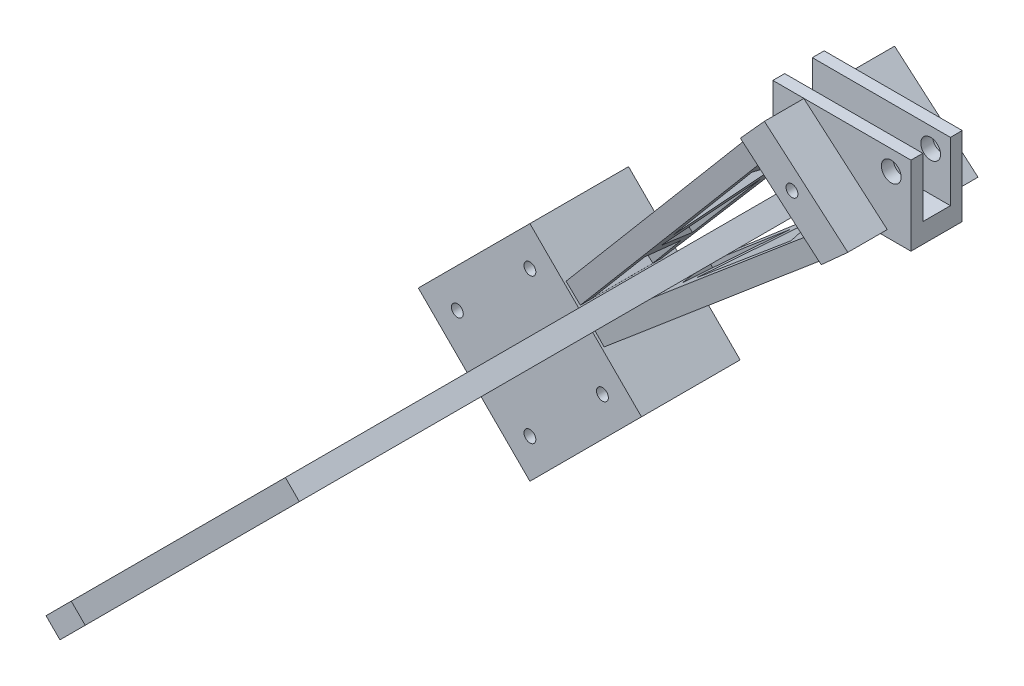
SolidWorks part; units mm, degrees
ref_plane "Front Plane" through (0, 0, 0) normal (0, 0, 1) x (1, 0, 0)
ref_plane "Top Plane" through (0, 0, 0) normal (0, 1, 0) x (1, 0, 0)
ref_plane "Right Plane" through (0, 0, 0) normal (1, 0, 0) x (0, 0, -1)
sketch "Sketch10" plane through (0, 0, 0) normal (0, 0, 1) x (1, 0, 0)
  line L1 (-17.5, 10) -> (17.5, 10)
  line L2 (-17.5, 10) -> (-17.5, -10)
  line L3 (-17.5, -10) -> (17.5, -10)
  line L4 (17.5, 10) -> (17.5, -10)
  line L5 (-17.5, 10) -> (17.5, -10) construction
  line L6 (-17.5, -10) -> (17.5, 10) construction
  point P0 (0, 0)
  dimension "D1" = 35
  dimension "D2" = 20
extrude "Boss-Extrude9" add sketch "Sketch10" along normal mid plane 13
sketch "Sketch11" plane through (-17.5, 0, 0) normal (-1, 0, 0) x (0, 0, 1)
  line L0 (6.5, 10) -> (-6.5, 10) construction
  line L2 (3.5, -5) -> (3.5, 10)
  line L3 (3.5, 10) -> (-3.5, 10)
  line L4 (-3.5, -5) -> (-3.5, 10)
  line L5 (1.75, -5) -> (-3.5, 10) construction
  line L6 (3.5, 10) -> (-1.75, -5) construction
  line L7 (-3.5, -5) -> (3.5, -5)
  point P0 (0, 0)
  dimension "D2" = 7
extrude "Cut-Extrude4" cut sketch "Sketch11" against normal through all both and the other way through all
sketch "Sketch12" plane through (0, 0, 0) normal (0, 0, 1) x (1, 0, 0)
  line L0 (0, 0) -> (-69.4425, -69.4425) construction
  line L1 (-17.5, -10) -> (17.5, -10) construction
  dimension "D1" = 135
sketch "Sketch14" plane through (0, 0, 0) normal (0, 1, 0) x (1, 0, 0)
  line L0 (0, 0) -> (0, -5.7548) construction
ref_plane "Plane2" through (0, 0, 0) normal (-0.7071, 0.7071, 0) x (0.7071, 0.7071, 0)
sketch "Sketch15" plane through (0, 0, 0) normal (-0.7071, 0.7071, 0) x (0.7071, 0.7071, 0)
  line L0 (-14.7751, 12.5) -> (-161.0806, 46.4618)
  line L2 (-161.0806, 46.4618) -> (-161.0806, 26.4618)
  line L3 (-161.0806, 26.4618) -> (-14.7751, -12.5)
  line L9 (-14.7751, -12.5) -> (-14.7751, 12.5)
  line L10 (-19.4454, -6.5) -> (5.3033, -6.5) construction
  dimension "D1" = 6
  dimension "D2" = 20
  dimension "D3" = 25
  dimension "D4" = 6
sketch "Sketch16" plane through (0, 0, -6.5) normal (0, 0, -1) x (-1, 0, 0)
  line L0 (111.7225, -116.0799) -> (-9.2412, -6.9169) construction
sketch "Sketch17" plane through (0, -10, 0) normal (0, -1, 0) x (1, 0, 0)
  line L0 (9.2412, -6.5) -> (9.2412, 5.7904)
  line L1 (-111.7225, -6.5) -> (9.2412, -6.5) construction
  line L2 (-17.5, -6.5) -> (17.5, -6.5) construction
ref_plane "Plane3" through (0, -6.9169, 0) normal (0, -1, 0) x (-1, 0, 0)
sketch "Sketch18" plane through (0, -6.9169, 0) normal (0, -1, 0) x (-1, 0, 0)
  line L0 (-9.2412, 6.5) -> (-9.2412, -5.7904) construction
  line L1 (-9.2412, 6.5) -> (-9.2412, -5.7904)
ref_plane "Plane4" through (7.5883, -8.4086, 0) normal (0.67, -0.7424, 0) x (-0.7424, -0.67, 0)
sketch "Sketch19" plane through (7.5883, -8.4086, 0) normal (0.67, -0.7424, 0) x (-0.7424, -0.67, 0)
  line L0 (-6.8066, 12.5) -> (-6.8066, 6.5)
  line L1 (-6.8066, 6.5) -> (5.9593, 6.5)
  line L2 (5.9593, 6.5) -> (5.9593, -6.5)
  line L3 (5.9593, -6.5) -> (-9.0214, -6.5)
  line L4 (-9.0214, -6.5) -> (-9.0214, -14.5)
  line L5 (-9.0214, -14.5) -> (143.1934, 27.2106)
  line L6 (143.1934, 27.2106) -> (143.1934, 47.5163)
  line L7 (143.1934, 47.5163) -> (-6.8066, 12.5)
  line L8 (23.4169, 15.4474) -> (23.4169, -2.9326)
  line L9 (23.4169, -2.9326) -> (48.1378, 21.7883)
  line L10 (48.1378, 21.7883) -> (23.4169, 15.4474)
  line L11 (34.1032, 0) -> (57.4554, 23.3522)
  line L12 (57.4554, 23.3522) -> (87.1388, 15.4474)
  line L13 (87.1388, 15.4474) -> (34.1032, 0)
  line L14 (69.5714, 26.3553) -> (96.9071, 19.0757)
  line L15 (96.9071, 19.0757) -> (112.2713, 37.3848)
  line L16 (69.5714, 26.3553) -> (112.2713, 37.3848)
  line L17 (116.6067, 37.3848) -> (103.0021, 19.0757)
  line L18 (103.0021, 19.0757) -> (136.677, 28.2302)
  line L19 (136.677, 28.2302) -> (136.677, 43.713)
  line L20 (136.677, 43.713) -> (116.6067, 37.3848)
  point P2 (5.9593, 0)
  dimension "D1" = 6
  dimension "D2" = 8
  dimension "D3" = 13
  dimension "D4" = 150
extrude "Boss-Extrude10" add sketch "Sketch19" along normal mid plane 5
mirror "Mirror3" about plane through (0, 0, 0) normal (-0.7071, 0.7071, 0) of "Boss-Extrude10"
sketch "Sketch20" plane through (0, 0, -6.5) normal (0, 0, -1) x (-1, 0, 0)
  line L0 (-13.5282, -10) -> (16.0112, 15.4294)
  line L1 (-9.5564, -10) -> (-17.5, -10) construction
  line L2 (16.0112, 15.4294) -> (-17.5, 15.4294)
  line L3 (-17.5, 15.4294) -> (-17.5, -10)
  line L4 (-17.5, -10) -> (-13.5282, -10)
  point P5 (16.0112, 15.4294)
extrude "Cut-Extrude5" cut sketch "Sketch20" along normal blind 20
sketch "Sketch21" plane through (0, 0, 6.5) normal (0, 0, 1) x (1, 0, 0)
  line L4 (-16.0112, 15.4294) -> (13.5282, -10)
  line L5 (17.5, 15.4294) -> (-16.0112, 15.4294)
  line L6 (17.5, -10) -> (17.5, 15.4294)
  line L7 (13.5282, -10) -> (17.5, -10)
  line L8 (-16.0112, 15.4294) -> (13.5282, -10)
  line L9 (17.5, 17.9422) -> (-16.0112, 15.4294)
  line L10 (17.5, -10) -> (17.5, 17.9422)
  line L11 (13.5282, -10) -> (17.5, -10)
  point P2 (17.5, 15.4294)
  point P3 (17.5, 17.9422)
  dimension "D1" = 0
extrude "Cut-Extrude6" cut sketch "Sketch21" along normal blind 20
sketch "Sketch22" plane through (0, 0, -6.5) normal (0, 0, -1) x (-1, 0, 0)
  line L0 (-4.7513, -14.3363) -> (15.7317, 3.2051)
  line L1 (97.0423, -106.1994) -> (-11.4954, -8.2501) construction
  line L2 (9.6454, 9.9493) -> (17.5, 1.2456) construction
  line L3 (15.7317, 3.2051) -> (9.6454, 9.9493)
  line L4 (9.6454, 9.9493) -> (-11.4954, -8.2501)
  line L5 (-11.4954, -8.2501) -> (-4.7513, -14.3363)
extrude "Boss-Extrude11" add sketch "Sketch22" along normal blind 10
mirror "Mirror5" about plane through (0, 0, 0) normal (0, 0, 1) of "Boss-Extrude11"
sketch "Sketch23" plane through (0, 0, -16.5) normal (0, 0, -1) x (-1, 0, 0)
  circle A0 centre (2.6614, -1.7871) radius 1.5
  point P4 (5.9862, 1.2179)
  point P5 (-1.735, -5.6686)
  point P6 (0, -4.5879)
  point P7 (2.6614, -1.7871)
  point P8 (0, 0)
  dimension "D1" = 3
extrude "Cut-Extrude7" cut sketch "Sketch23" against normal through all
sketch "Sketch24" plane through (0, 0, 0) normal (0, 0, 1) x (1, 0, 0)
  line L1 (-82.1618, -111.8669) -> (-110.446, -140.1512)
  line L2 (-82.1618, -111.8669) -> (-110.446, -83.5826)
  line L3 (-110.446, -83.5826) -> (-138.7303, -111.8669)
  line L4 (-110.446, -140.1512) -> (-138.7303, -111.8669)
  point P0 (-107.7418, -108.8087)
  dimension "D1" = 40
ref_plane "Plane5" through (0, 0, -37.3634) normal (0, 0, 1) x (1, 0, 0)
sketch "Sketch25" plane through (0, 0, -37.3634) normal (0, 0, 1) x (1, 0, 0)
  line L0 (-96.3039, -97.7248) -> (-124.5882, -126.009) construction
  line L1 (-96.3039, -126.009) -> (-124.5882, -97.7248) construction
  line L4 (-110.446, -140.1512) -> (-82.1618, -111.8669)
  line L5 (-138.7303, -111.8669) -> (-110.446, -140.1512)
  line L6 (-110.446, -83.5826) -> (-138.7303, -111.8669)
  line L7 (-82.1618, -111.8669) -> (-110.446, -83.5826)
  line L8 (-110.446, -140.1512) -> (-82.1618, -111.8669)
  line L9 (-138.7303, -111.8669) -> (-110.446, -140.1512)
  line L10 (-110.446, -83.5826) -> (-138.7303, -111.8669)
  line L11 (-82.1618, -111.8669) -> (-110.446, -83.5826)
  circle A0 centre (-110.446, -93.4821) radius 1.5
  circle A1 centre (-92.0613, -111.8669) radius 1.5
  circle A2 centre (-110.446, -130.2517) radius 1.5
  circle A3 centre (-128.8308, -111.8669) radius 1.5
  dimension "D2" = 3
  dimension "D3" = 7
  dimension "D4" = 7
  dimension "D1" = 0
extrude "Boss-Extrude12" add sketch "Sketch25" along normal mid plane 25
sketch "Sketch27" plane through (-17.5, 0, 0) normal (-1, 0, 0) x (0, 0, 1)
  line L0 (-3.5, 10) -> (-3.5, -5)
  line L1 (-3.5, -5) -> (3.5, -5)
  line L2 (3.5, -5) -> (3.5, 10)
  line L3 (3.5, 10) -> (-3.5, 10)
  dimension "D1" = 7
  dimension "D2" = 15
extrude "Cut-Extrude9" cut sketch "Sketch27" against normal blind 20
sketch "Sketch28" plane through (-17.5, 0, 0) normal (1, 0, 0) x (0, 0, -1)
  line L4 (3.5, 1.2456) -> (-3.5, 1.2456)
  line L5 (-3.5, 1.2456) -> (-3.5, -5)
  line L6 (-3.5, -5) -> (3.5, -5)
  line L7 (3.5, -5) -> (3.5, 1.2456)
  line L8 (3.5, 1.2456) -> (-3.5, 1.2456)
  line L9 (-3.5, 1.2456) -> (-3.5, -5)
  line L10 (-3.5, -5) -> (3.5, -5)
  line L11 (3.5, -5) -> (3.5, 1.2456)
  dimension "D1" = 0
extrude "Cut-Extrude10" cut sketch "Sketch28" against normal blind 20
ref_plane "Plane6" through (0.7104, -0.7104, 0) normal (0.7071, -0.7071, 0) x (0, 0, -1)
sketch "Sketch29" plane through (0.7104, -0.7104, 0) normal (0.7071, -0.7071, 0) x (0, 0, -1)
  line L0 (25.9409, -150.294) -> (-9.7018, -150.294)
  line L1 (-9.7018, -150.294) -> (-104.0591, -136.7811)
  line L2 (-104.0591, -136.7811) -> (-104.0591, -145.8352)
  line L3 (-104.0591, -145.8352) -> (-19.3486, -180.9884)
  line L4 (-19.3486, -180.9884) -> (25.9409, -162.5195)
  line L5 (25.9409, -162.5195) -> (25.9409, -150.294)
  line L22 (-9.7018, -155.4838) -> (-16.9268, -176.0465)
  line L23 (-16.9268, -176.0465) -> (15.2881, -162.5195)
  line L24 (15.2881, -162.5195) -> (15.2881, -155.4838)
  line L25 (15.2881, -155.4838) -> (-9.7018, -155.4838)
  line L26 (-16.7414, -155.1411) -> (-23.9664, -175.7038)
  line L27 (-23.9664, -175.7038) -> (-44.3437, -149.9513)
  line L28 (-44.3437, -149.9513) -> (-16.7414, -155.1411)
  line L29 (-36.176, -169.283) -> (-51.2015, -150.294)
  line L30 (-51.2015, -150.294) -> (-77.244, -152.8889)
  line L31 (-77.244, -152.8889) -> (-36.176, -169.283)
  line L32 (-85.4691, -150.294) -> (-60.6355, -147.8196)
  line L33 (-60.6355, -147.8196) -> (-86.1945, -143.014)
  line L34 (-86.1945, -143.014) -> (-85.4691, -150.294)
  dimension "D1" = 130
extrude "Boss-Extrude13" add sketch "Sketch29" along normal mid plane 5
sketch "Sketch30" plane through (2.4782, -2.4782, 0) normal (0.7071, -0.7071, 0) x (0, 0, -1)
  line L0 (-41.0591, -146.7811) -> (-2.2007, -12.5918)
  line L1 (-2.2007, -12.5918) -> (-4.9686, -11.7903)
  line L2 (-4.9686, -11.7903) -> (-44.0591, -146.7811)
  line L3 (-44.0591, -146.7811) -> (-41.0591, -146.7811)
  line L4 (-104.0591, -136.7811) -> (-104.0591, -145.8352) construction
  line L6 (-9.7018, -150.294) -> (-104.0591, -136.7811) construction
  point P6 (-41.072, -145.8015)
  dimension "D1" = 60
  dimension "D2" = 3
  dimension "D3" = 10
  dimension "D4" = 10
  dimension "D5" = 82
extrude "Boss-Extrude14" add sketch "Sketch30" against normal up to surface (5 mm away) up to face at (-110.3232, -108.2085, 31.2403)
sketch "Sketch31" plane through (0, 0, -6.5) normal (0, 0, -1) x (-1, 0, 0)
  line L0 (-17.5, 10) -> (17.5, 10) construction
  line L1 (-17.5, -10) -> (-17.5, 10) construction
  circle A0 centre (-12.5, 5) radius 2.5
  dimension "D1" = 5
  dimension "D2" = 5
  dimension "D3" = 5
extrude "Cut-Extrude11" cut sketch "Sketch31" against normal through all both and the other way through all
